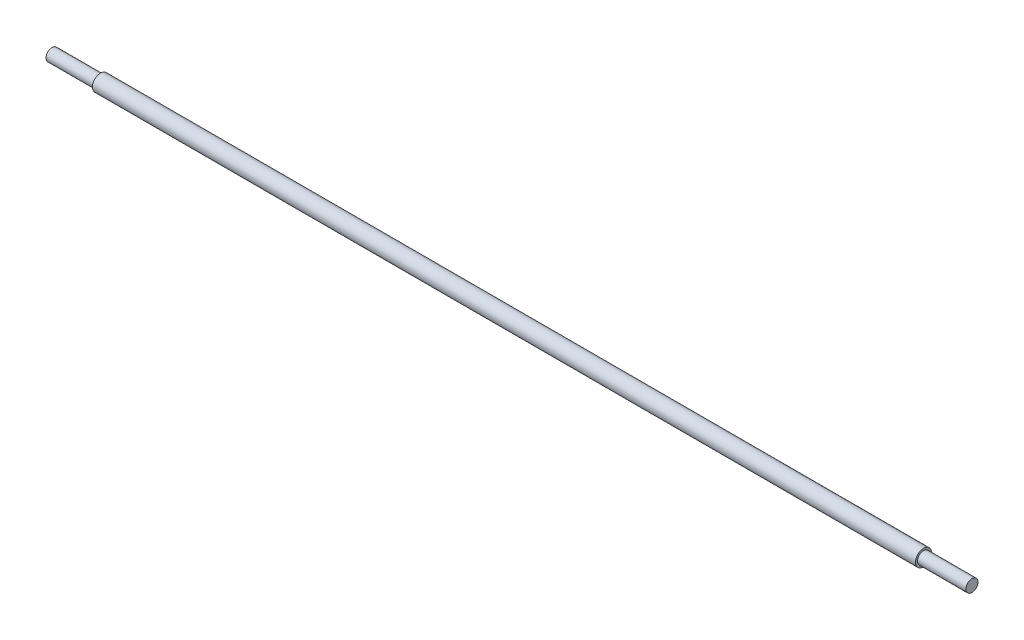
SolidWorks part; units mm, degrees
material "Plain Carbon Steel"
ref_plane "Front Plane" through (0, 0, 0) normal (0, 0, 1) x (1, 0, 0)
ref_plane "Top Plane" through (0, 0, 0) normal (0, 1, 0) x (1, 0, 0)
ref_plane "Right Plane" through (0, 0, 0) normal (1, 0, 0) x (0, 0, -1)
sketch "Sketch2" plane through (0, 0, 0) normal (0, 1, 0) x (1, 0, 0)
  line L0 (-723.9, 0) -> (723.9, 0)
  line L1 (-723.9, 0) -> (-723.9, 9.525)
  line L2 (-723.9, 9.525) -> (-647.7, 9.525)
  line L3 (-647.7, 9.525) -> (-647.7, 12.7)
  line L4 (-647.7, 12.7) -> (647.7, 12.7)
  line L5 (0, 12.7) -> (0, 0) construction
  line L6 (647.7, 9.525) -> (647.7, 12.7)
  line L7 (723.9, 9.525) -> (647.7, 9.525)
  line L8 (723.9, 0) -> (723.9, 9.525)
  point P4 (0, 0)
  dimension "D1" = 1447.8
  dimension "D2" = 9.525
  dimension "D3" = 12.7
  dimension "D4" = 76.2
revolve "Revolve1" add sketch "Sketch2" angle 360 about L0
